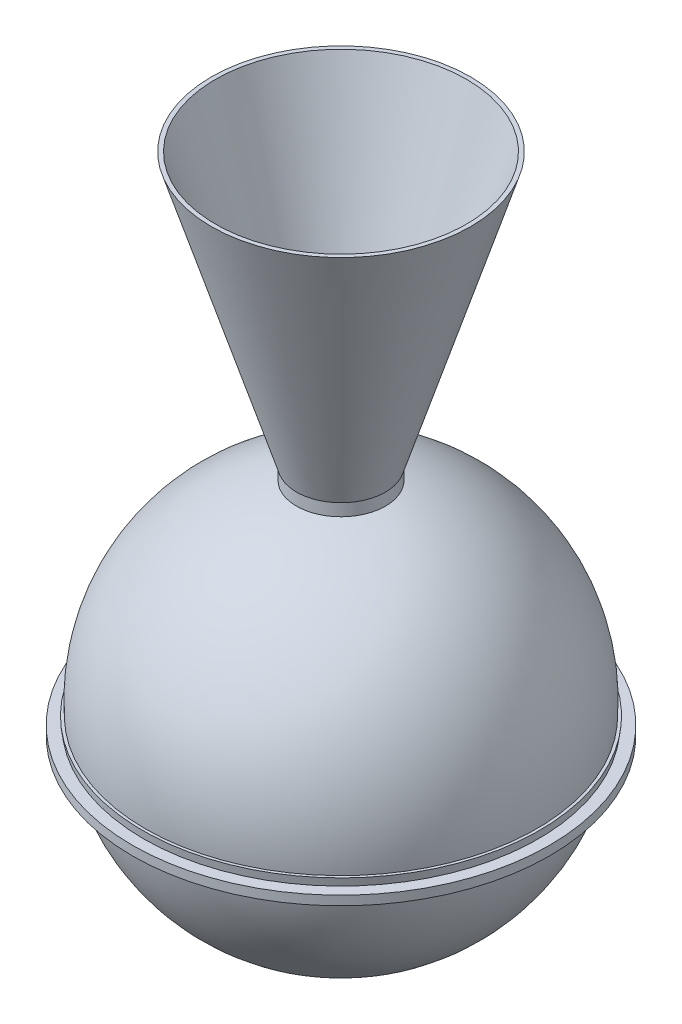
SolidWorks part; units mm, degrees
material "Main engine"
ref_plane "Front Plane" through (0, 0, 0) normal (0, 0, 1) x (1, 0, 0)
ref_plane "Top Plane" through (0, 0, 0) normal (0, 1, 0) x (1, 0, 0)
ref_plane "Right Plane" through (0, 0, 0) normal (1, 0, 0) x (0, 0, -1)
sketch "Sketch1" plane through (0, 0, 0) normal (0, 0, 1) x (1, 0, 0)
  line L0 (0, -286.7426) -> (0, 374.65) construction
  line L1 (0, -54.5546) -> (789.9922, -54.5546) construction
  line L2 (0, -43.0646) -> (604.4518, -43.0646) construction
  line L3 (0, -31.5646) -> (789.9922, -31.5646) construction
  line L4 (0, -20.0746) -> (772.2976, -20.0746) construction
  line L5 (0, 286.7426) -> (650.7423, 286.7426) construction
  line L6 (0, 298.2326) -> (662.0662, 298.2326) construction
  line L7 (0, 697.0326) -> (945.2276, 697.0326) construction
  line L8 (64.35, 298.2326) -> (64.35, 136.246) construction
  line L9 (305, -31.5646) -> (305, 38.8383) construction
  line L10 (305, -31.5646) -> (305, -191.589) construction
  line L11 (290.039, -20.0746) -> (285.5051, -54.5546) construction
  line L12 (281.5051, -54.5546) -> (285.5051, -54.5546)
  line L13 (285.5051, -54.5546) -> (287.016, -43.0646)
  line L14 (287.016, -43.0646) -> (305, -43.0646)
  line L15 (305, -43.0646) -> (305, -31.5646)
  line L16 (305, -31.5646) -> (288.5282, -31.5646)
  line L17 (288.5282, -31.5646) -> (290.039, -20.0746)
  line L18 (286.039, -20.0746) -> (290.039, -20.0746)
  line L19 (64.35, 279.4287) -> (64.35, 298.2326)
  line L20 (64.35, 298.2326) -> (188.95, 697.0326)
  line L21 (281.5051, -54.5546) -> (0, 0) construction
  line L22 (286.039, -20.0746) -> (0, 0) construction
  line L23 (64.35, 298.2326) -> (-4.4792, 396.5309) construction
  line L24 (64.35, 298.2326) -> (85.1878, 180.0557) construction
  line L25 (81.8673, 198.8872) -> (123.0556, 254.5598) construction
  line L26 (109.8229, 260.0598) -> (123.0556, 254.5598)
  line L27 (6.4888, 380.867) -> (82.726, 357.0477) construction
  line L28 (70.6861, 360.8094) -> (184.95, 697.0326)
  line L29 (184.95, 697.0326) -> (188.95, 697.0326)
  line L30 (25.4, -355.6) -> (25.4, 520.7) construction
  line L31 (25.4, -259.3413) -> (125.98, 228.1055)
  line L32 (290.039, -20.0746) -> (290.039, -87.1284) construction
  circle A0 centre (0, 0) radius 286.7426 construction
  arc A1 (0, -286.7426) -> (281.5051, -54.5546) centre (0, 0) ccw
  arc A2 (286.039, -20.0746) -> (64.35, 279.4287) centre (0, 0) ccw
  circle A3 centre (0, 0) radius 282.7426 construction
  circle A4 centre (64.36, 298.2326) radius 33.626 construction
  circle A5 centre (6.4888, 380.867) radius 67.2577 construction
  circle A6 centre (81.8673, 198.8872) radius 67.2574 construction
  arc A7 (45.0662, 325.7727) -> (70.1881, 265.1231) centre (64.35, 298.2326) ccw
  arc A8 (70.1881, 265.1231) -> (109.8229, 260.0598) centre (81.8673, 198.8872) cw
  arc A9 (45.0662, 325.7727) -> (70.6861, 360.8094) centre (6.4888, 380.867) ccw
  arc A10 (0, -282.7426) -> (123.0556, 254.5598) centre (0, 0) ccw
  circle A11 centre (0, 0) radius 260.5822 construction
  arc A12 (25.4, -259.3413) -> (125.98, 228.1055) centre (0, 0) ccw
  point P5 (0, -54.5546)
  point P8 (0, -20.0746)
  point P9 (0, -43.0646)
  point P10 (0, -31.5646)
  point P17 (0, 286.7426)
  point P20 (0, 298.2326)
  point P23 (64.35, 298.2326)
  point P24 (30.734, 298.2326)
  point P25 (0, 697.0326)
  point P28 (188.95, 697.0326)
  point P32 (285, -31.5646)
  point P33 (305, -31.5646)
  point P38 (290.039, -20.0746)
  point P39 (285.5051, -54.5546)
  point P42 (287.016, -43.0646)
  point P43 (288.5282, -31.5646)
  point P44 (305, -43.0646)
  point P46 (64.35, 279.4287)
  point P49 (286.039, -20.0746)
  point P51 (0, -282.7426)
  point P54 (123.0556, 254.5598)
  point P55 (64.36, 298.2326)
  point P58 (184.95, 697.0326)
  point P59 (6.4888, 380.867)
  point P63 (81.8673, 198.8872)
  point P78 (25.4, -259.3413)
  dimension "D1" = 232.188
  dimension "D15" = 100.878
  dimension "D2" = 34.48
  dimension "D3" = 11.49
  dimension "D4" = 11.49
  dimension "D5" = 11.49
  dimension "D6" = 64.35
  dimension "D7" = 30.734
  dimension "D8" = 398.8
  dimension "D9" = 188.95
  dimension "D10" = 20
  dimension "D11" = 4
  dimension "D12" = 4
  dimension "D13" = 4
  dimension "WHALL_C" = 4
  dimension "D14" = 100.878
  dimension "R_INTERNAL" = 33.626
  dimension "D16" = 305
  dimension "D17" = 11.5
  dimension "D18" = 14.961
revolve "Revolve-Thin2" add sketch "Sketch1" angle 360 about L0
equation "\"D13@Sketch1\" = \"WHALL_C\""
equation "\"D14@Sketch1\" = \"R_INTERNAL\"*3"
equation "\"D15@Sketch1\" = \"R_INTERNAL\"*3"
